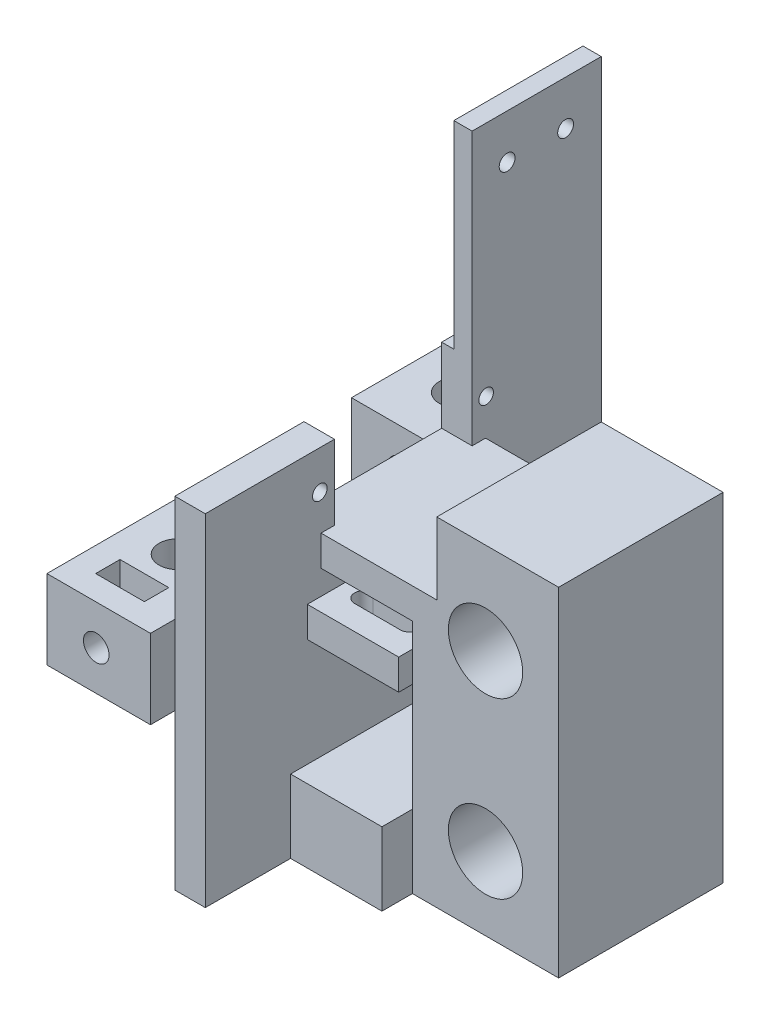
SolidWorks part; units mm, degrees
ref_plane "Front Plane" through (0, 0, 0) normal (0, 0, 1) x (1, 0, 0)
ref_plane "Top Plane" through (0, 0, 0) normal (0, 1, 0) x (1, 0, 0)
ref_plane "Right Plane" through (0, 0, 0) normal (1, 0, 0) x (0, 0, -1)
sketch "Sketch1" plane through (0, 0, 0) normal (0, 0, 1) x (1, 0, 0)
  line L0 (0, -26.25) -> (0, 26.25)
  line L1 (-28.3964, 0) -> (35.8693, 0) construction
  line L2 (0, 26.25) -> (24, 26.25)
  line L3 (24, 26.25) -> (24, -26.25)
  line L4 (24, -26.25) -> (0, -26.25)
  circle A0 centre (12, 14.25) radius 6.1
  circle A1 centre (12, -14.25) radius 6.1
  point P8 (0, 0)
  point P13 (12, 26.25)
  dimension "D2" = 12.2
  dimension "D1" = 26.25
  dimension "D3" = 28.5
  dimension "D4" = 12
extrude "Boss-Extrude1" add sketch "Sketch1" along normal mid plane 27
ref_plane "Plane1" through (0, 5.5, 0) normal (0, 1, 0) x (1, 0, 0)
sketch "Sketch2" plane through (0, 5.5, 0) normal (0, 1, 0) x (1, 0, 0)
  line L0 (0, 0) -> (-10.1748, 0) construction
  line L1 (0, 7) -> (0, -7)
  line L2 (0, 7) -> (-4, 7) construction
  line L3 (-4, 7) -> (-4, -7) construction
  line L4 (-4, -7) -> (0, -7) construction
  line L5 (0, 7) -> (-15, 7) construction
  line L6 (-15, 7) -> (-15, 15.75) construction
  line L7 (-15, 15.75) -> (0, 15.75) construction
  line L8 (-4, 7) -> (-11, 7)
  line L9 (-7.5, 7) -> (-7.5, 16.2228) construction
  line L10 (-11, 7) -> (-15, 7)
  line L11 (-15, 7) -> (-15, 15.75)
  line L12 (-15, 15.75) -> (0, 15.75)
  line L13 (0, 15.75) -> (0, 7)
  line L14 (-4, 7) -> (0, 7)
  line L15 (-11.25, 10.25) -> (-3.75, 10.25) construction
  line L16 (-11.25, 11.75) -> (-3.75, 11.75)
  line L17 (-11.25, 8.75) -> (-3.75, 8.75)
  line L18 (-15, -15.75) -> (0, -15.75) construction
  line L19 (-15, -7) -> (-15, -15.75) construction
  line L20 (0, -7) -> (-15, -7) construction
  line L21 (0, -7) -> (-4, -7) construction
  line L22 (-4, -7) -> (0, -7)
  line L23 (0, -15.75) -> (0, -7)
  line L24 (-15, -15.75) -> (0, -15.75)
  line L25 (-15, -7) -> (-15, -15.75)
  line L26 (-11, -7) -> (-15, -7)
  line L27 (-4, -7) -> (-11, -7)
  line L28 (-11.25, -10.25) -> (-3.75, -10.25) construction
  line L29 (-11.25, -11.75) -> (-3.75, -11.75)
  line L30 (-11.25, -8.75) -> (-3.75, -8.75)
  arc A0 (-11.25, 11.75) -> (-11.25, 8.75) centre (-11.25, 10.25) ccw
  arc A1 (-3.75, 8.75) -> (-3.75, 11.75) centre (-3.75, 10.25) ccw
  arc A2 (-11.25, -11.75) -> (-11.25, -8.75) centre (-11.25, -10.25) cw
  arc A3 (-3.75, -8.75) -> (-3.75, -11.75) centre (-3.75, -10.25) cw
  point P5 (0, 0)
  point P17 (-7.5, 10.25)
  point P28 (-7.5, -10.25)
  dimension "D3" = 4
  dimension "D1" = 14
  dimension "D2" = 7
  dimension "D4" = 3
  dimension "D5" = 1.75
extrude "Boss-Extrude2" add sketch "Sketch2" along normal blind 3 and the other way blind 2 contours L22 L27 L26 L25 L24 L23 L30 A3 L29 A2 | L8 L14 L13 L12 L11 L10 A1 L17 A0 L16
sketch "Sketch3" plane through (0, 0, 0) normal (-1, 0, 0) x (0, 0, 1)
  line L0 (-13.5, -8.25) -> (-13.5, -26.25)
  line L1 (-13.5, 3.5) -> (-13.5, -26.25) construction
  line L2 (-13.5, -26.25) -> (13.5, -26.25)
  line L3 (13.5, -26.25) -> (13.5, -8.25)
  line L4 (13.5, 3.5) -> (13.5, -26.25) construction
  line L5 (13.5, -8.25) -> (-13.5, -8.25)
  line L6 (-13.5, 26.25) -> (-13.5, 12.5)
  line L7 (-13.5, 26.25) -> (-13.5, 8.5) construction
  line L8 (-13.5, 12.5) -> (13.5, 12.5)
  line L9 (13.5, 26.25) -> (13.5, 8.5) construction
  line L10 (13.5, 12.5) -> (13.5, 26.25)
  line L11 (13.5, 26.25) -> (-13.5, 26.25)
  line L12 (-8.75, 8.5) -> (-8.75, 12.5)
  line L13 (-8.75, 8.5) -> (-7, 8.5)
  line L14 (-7, 8.5) -> (-7, 5.5)
  line L15 (14.85, 5.5) -> (-14.85, 5.5) construction
  line L16 (-7, 8.5) -> (-7, 3.5) construction
  line L17 (-7, 5.5) -> (7, 5.5)
  line L18 (7, 8.5) -> (7, 3.5) construction
  line L19 (7, 5.5) -> (7, 8.5)
  line L20 (7, 8.5) -> (8.75, 8.5)
  line L21 (13.5, 8.5) -> (7, 8.5) construction
  line L22 (8.75, 8.5) -> (8.75, 12.5)
  line M5 (-13.5, 26.25) -> (-13.5, 8.5)
  line M6 (-13.5, 8.5) -> (-7, 8.5)
  line M7 (-7, 8.5) -> (-7, 3.5)
  line M9 (-13.5, 3.5) -> (-13.5, -26.25)
  line M10 (-13.5, -26.25) -> (13.5, -26.25)
  line M11 (13.5, -26.25) -> (13.5, 3.5)
  line M13 (7, 3.5) -> (7, 8.5)
  line M14 (7, 8.5) -> (13.5, 8.5)
  line M15 (13.5, 8.5) -> (13.5, 26.25)
  line M16 (13.5, 26.25) -> (-13.5, 26.25)
  dimension "D1" = 1.75
extrude "Boss-Extrude3" add sketch "Sketch3" along normal up to surface (15 mm away) contours L8 M5 M15 M16 | L22 L8 L12 L17 M14 M6 M7 M13 | L5 M11 M9 M10 up to face at (-15, 6, -11.375)
sketch "Sketch4" plane through (-15, 0, 0) normal (-1, 0, 0) x (0, 0, 1)
  line L0 (-13.5, 26.25) -> (-13.5, -26.25)
  line L1 (-13.5, -26.25) -> (13.5, -26.25)
  line L2 (13.5, -26.25) -> (13.5, 26.25)
  line L3 (13.5, 26.25) -> (-13.5, 26.25)
  line L4 (-16, 29.5) -> (16, 29.5)
  line L5 (-16, 29.5) -> (-16, 17.5)
  line L6 (-16, 17.5) -> (16, 17.5)
  line L7 (16, 17.5) -> (16, 29.5)
  line L8 (-13.5, 12.5) -> (-8.75, 12.5) construction
  point P10 (0, 29.5)
  point P13 (0, 26.25)
  line M8 (13.5, 26.25) -> (-13.5, 26.25)
  line M9 (-15.75, 8.5) -> (-15.75, 3.5)
  dimension "D1" = 32
  dimension "D2" = 12
  dimension "D3" = 5
extrude "Cut-Extrude2" cut sketch "Sketch4" against normal blind 18 contours L6 L7 L4 L5 L2 M9 M8 | L6 L2 M9 M8
ref_plane "Plane2" through (-15, 0, 0) normal (-1, 0, 0) x (0, 0, 1)
sketch "Sketch6" plane through (-15, 0, 0) normal (-1, 0, 0) x (0, 0, 1)
  line L0 (-32.5, 29.75) -> (32.5, 29.75)
  line L1 (32.5, 29.75) -> (32.5, -26.25)
  line L2 (32.5, -26.25) -> (-32.5, -26.25)
  line L3 (-32.5, -26.25) -> (-32.5, 29.75)
  line L4 (13.5, 26.25) -> (-13.5, 26.25) construction
  line L8 (-13.5, -26.25) -> (13.5, -26.25) construction
  point P6 (0, 26.25)
  point P7 (0, 29.75)
  point P10 (0, -26.25)
  dimension "D1" = 65
  dimension "D2" = 56
extrude "Boss-Extrude4" add sketch "Sketch6" along normal blind 22
sketch "Sketch7" plane through (0, 29.75, 0) normal (0, 1, 0) x (1, 0, 0)
  line L0 (-29, 23) -> (-29, -23) construction
  line L1 (3, 11.3) -> (3, -11.3)
  line L2 (-15, -32.5) -> (-15, 32.5) construction
  line L3 (-15, -13.5) -> (-15, 13.5) construction
  line L4 (-37, 32.5) -> (-37, -32.5)
  line L5 (-15, 0) -> (7.9194, 0) construction
  line L6 (-15, 16) -> (-12.5, 16)
  line L7 (-27, 7.7) -> (-23.8, 7.7)
  line L8 (-27, 3.1) -> (-23.8, 3.1)
  line L9 (3, 11.3) -> (-12.5, 11.3)
  line L10 (-12.5, 11.3) -> (-12.5, 16)
  line L11 (-15, 16) -> (-15, -16)
  line L12 (-15, -16) -> (-12.5, -16)
  line L13 (-12.5, -11.3) -> (-12.5, -16)
  line L14 (3, -11.3) -> (-12.5, -11.3)
  line L15 (-15, 11.3) -> (-19.4, 11.3)
  line L16 (-19.4, 11.3) -> (-19.4, -11.3)
  line L17 (-19.4, -11.3) -> (-15, -11.3)
  line L18 (-19.4, 11.3) -> (-23.8, 11.3)
  line L19 (-23.8, 11.3) -> (-23.8, -3.4)
  line L20 (-23.8, -3.4) -> (-19.4, -3.4)
  line L21 (-23.8, 11.3) -> (-27, 11.3) construction
  line L22 (-27, 11.3) -> (-27, 5.4) construction
  line L23 (-27, 7.7) -> (-27, 3.1)
  circle A0 centre (-29, 23) radius 3.1
  circle A1 centre (-29, -23) radius 3.1
  point P4 (-37, 0)
  point P5 (-29, 0)
  point P26 (3, 0)
  point P37 (-27, 5.4)
  dimension "D1" = 6.2
  dimension "D2" = 6.2
  dimension "D3" = 46
  dimension "D4" = 16
  dimension "D5" = 4.4
  dimension "D6" = 11.3
  dimension "D7" = 15.5
  dimension "D8" = 3.2
  dimension "D9" = 5.9
  dimension "D10" = 4.6
  dimension "D11" = 4.4
  dimension "D12" = 14
extrude "Cut-Extrude3" cut sketch "Sketch7" against normal through all contours A0 | A1
sketch "Sketch8" plane through (0, 29.75, 0) normal (0, 1, 0) x (1, 0, 0)
  line L1 (-20, -32.5) -> (-37, -32.5)
  line L2 (-37, -32.5) -> (-37, 32.5)
  line L3 (-37, 32.5) -> (-20, 32.5)
  line L4 (-37, -32.5) -> (-15, -32.5) construction
  line L5 (-37, 32.5) -> (-15, 32.5) construction
  line L6 (-20, 32.5) -> (-20, -32.5)
  line L7 (-15, -13.5) -> (-15, 13.5) construction
  dimension "D1" = 5
extrude "Cut-Extrude4" cut sketch "Sketch8" against normal blind 17.5
sketch "Sketch10" plane through (0, -26.25, 0) normal (0, -1, 0) x (1, 0, 0)
  line L0 (-20, 32.5) -> (-37, 32.5) construction
  line L1 (-37, 32.5) -> (-37, -32.5) construction
  line L2 (-20, -32.5) -> (-20, 32.5) construction
  line L3 (-37, -32.5) -> (-20, -32.5) construction
  line L4 (-20, 32.5) -> (-37, 32.5)
  line L5 (-37, 32.5) -> (-37, -32.5)
  line L6 (-20, -32.5) -> (-20, 32.5)
  line L7 (-37, -32.5) -> (-20, -32.5)
sketch "Sketch11" plane through (-20, 0, 0) normal (-1, 0, 0) x (0, 0, 1)
  line L0 (-11.3, 29.75) -> (11.3, 29.75)
  line L1 (-32.5, 29.75) -> (32.5, 29.75) construction
  line L2 (-11.3, 29.75) -> (-11.3, 17.5)
  line L3 (-11.3, 17.5) -> (11.3, 17.5)
  line L4 (11.3, 17.5) -> (11.3, 29.75)
  point P2 (0, 29.75)
  point P5 (0, 29.75)
extrude "Cut-Extrude6" cut sketch "Sketch11" against normal up to surface (5 mm away) up to face at (-15, 9, 0)
sketch "Sketch12" plane through (0, 12.25, 0) normal (0, 1, 0) x (1, 0, 0)
  line L0 (-20, 13.5) -> (-37, 13.5)
  line L1 (-20, 32.5) -> (-20, -32.5) construction
  line L2 (-37, -32.5) -> (-37, 32.5) construction
  line L3 (-37, 13.5) -> (-37, -13.5)
  line L4 (-37, -13.5) -> (-20, -13.5)
  line L5 (-20, -13.5) -> (-20, 13.5)
extrude "Cut-Extrude7" cut sketch "Sketch12" against normal through all
sketch "Sketch13" plane through (0, -26.25, 0) normal (0, -1, 0) x (1, 0, 0)
  line L0 (-20, 32.5) -> (-37, 32.5) construction
  line L1 (-37, 32.5) -> (-37, -32.5) construction
  line L2 (-37, -32.5) -> (-20, -32.5) construction
  line L3 (-20, -32.5) -> (-20, 32.5) construction
  line L4 (-20, 32.5) -> (-37, 32.5)
  line L5 (-37, 32.5) -> (-37, -32.5)
  line L6 (-37, -32.5) -> (-20, -32.5)
  line L7 (-20, -32.5) -> (-20, 32.5)
extrude "Cut-Extrude8" cut sketch "Sketch13" against normal blind 25.5
sketch "Sketch16" plane through (0, -8.25, 0) normal (0, 1, 0) x (1, 0, 0)
  line L0 (0, -13.5) -> (-15, -13.5)
  line L2 (0, -13.5) -> (0, 13.5)
  line L3 (0, 13.5) -> (-15, 13.5)
  line L4 (-15, 13.5) -> (24, 13.5) construction
  line L5 (-15, -13.5) -> (-15, 13.5)
extrude "Cut-Extrude9" cut sketch "Sketch16" against normal blind 6
sketch "Sketch17" plane through (0, 0, -13.5) normal (0, 0, -1) x (-1, 0, 0)
  line L0 (0, -14.25) -> (0, -26.25)
  line L1 (15, -26.25) -> (-24, -26.25) construction
  line L2 (0, -26.25) -> (15, -26.25)
  line L3 (15, -26.25) -> (15, -14.25)
  line L4 (15, -14.25) -> (0, -14.25)
extrude "Boss-Extrude5" add sketch "Sketch17" along normal blind 5 and the other way blind 32
sketch "Sketch18" plane through (0, 0, -32.5) normal (0, 0, -1) x (-1, 0, 0)
  line L0 (28.9022, 25.3865) -> (28.9022, 12.25) construction
  line L1 (20, 12.25) -> (37, 12.25) construction
  line L2 (37, 12.25) -> (37, -0.75) construction
  line L3 (37, 5.75) -> (38.7662, 5.75) construction
  circle A0 centre (28.9022, 5.75) radius 2.1
  dimension "D1" = 4.2
  dimension "D2" = 0
  dimension "D3" = 0
sketch "Sketch19" plane through (0, 26.25, 0) normal (0, 1, 0) x (1, 0, 0)
  line L4 (3, 13.5) -> (3, -13.5)
  line L5 (3, -13.5) -> (24, -13.5)
  line L6 (24, -13.5) -> (24, 13.5)
  line L7 (24, 13.5) -> (3, 13.5)
  line L8 (3, 13.5) -> (3, -13.5)
  line L9 (3, -13.5) -> (24, -13.5)
  line L10 (24, -13.5) -> (24, 13.5)
  line L11 (24, 13.5) -> (3, 13.5)
  dimension "D1" = 0
extrude "Boss-Extrude6" add sketch "Sketch19" along normal blind 3.05
sketch "Sketch20" plane through (0, 0, 13.5) normal (0, 0, 1) x (1, 0, 0)
  line L0 (3, 17.5) -> (4, 17.5)
  line L1 (4, 17.5) -> (4, 29.3)
  line L2 (3, 29.3) -> (24, 29.3) construction
  line L3 (4, 29.3) -> (3, 29.3)
  line L4 (3, 29.3) -> (3, 17.5)
extrude "Cut-Extrude11" cut sketch "Sketch20" against normal through all
sketch "Sketch21" plane through (-15, 0, 0) normal (1, 0, 0) x (0, 0, -1)
  circle A0 centre (-13.7, 23.4) radius 1.2
  circle A1 centre (13.6, 23.4) radius 1.2
extrude "Cut-Extrude12" cut sketch "Sketch21" against normal blind 10
ref_plane "Plane3" through (0, 12.25, 0) normal (0, 1, 0) x (1, 0, 0)
sketch "Sketch22" plane through (0, 12.25, 0) normal (0, 1, 0) x (1, 0, 0)
  line L0 (-29, 23) -> (-29, 34.5) construction
  line L2 (-29, 30.5) -> (-29, 34.5) construction
  line L3 (-25, 30.5) -> (-33, 30.5)
  line L4 (-29, 30.5) -> (-29, 33.0319) construction
  line L5 (-25, 30.5) -> (-25, 34.5)
  line L7 (-33, 34.5) -> (-33, 30.5)
  line L8 (0, 0) -> (-75.4132, 0) construction
  line L9 (-33, -34.5) -> (-33, -30.5)
  line L10 (-25, -34.5) -> (-33, -34.5)
  line L11 (-25, -30.5) -> (-25, -34.5)
  line L12 (-25, -30.5) -> (-33, -30.5)
  line L13 (-25, 34.5) -> (-33, 34.5)
  dimension "D1" = 0
  dimension "D2" = 4
  dimension "D3" = 7.5
sketch "Sketch23" plane through (0, 0, -32.5) normal (0, 0, -1) x (-1, 0, 0)
  line L0 (20, -0.75) -> (20, 12.25)
  line L1 (9.35, 12.25) -> (-9.35, 12.25) construction
  line L2 (20, 12.25) -> (37, 12.25)
  line L3 (37, 12.25) -> (37, -0.75) construction
  line L4 (37, 12.25) -> (37, -0.75)
  line L5 (37, -0.75) -> (20, -0.75)
extrude "Boss-Extrude7" add sketch "Sketch23" along normal blind 4
sketch "Sketch24" plane through (0, 0, 32.5) normal (0, 0, 1) x (1, 0, 0)
  line L0 (-37, 12.25) -> (-37, -0.75)
  line L1 (-37, -0.75) -> (-20, -0.75)
  line L2 (-20, -0.75) -> (-20, 12.25)
  line L3 (0, 12.25) -> (-75.4132, 12.25) construction
  line L4 (-20, 12.25) -> (-37, 12.25)
extrude "Boss-Extrude8" add sketch "Sketch24" along normal blind 4
sketch "Sketch25" plane through (0, 0, -36.5) normal (0, 0, -1) x (-1, 0, 0)
  circle A0 centre (28.9022, 5.75) radius 2.1 construction
  circle A1 centre (28.9022, 5.75) radius 2.1
extrude "Cut-Extrude14" cut sketch "Sketch25" against normal through all
sketch "Sketch26" plane through (0, 12.25, 0) normal (0, 1, 0) x (1, 0, 0)
  line L8 (-33, -32.5) -> (-33, -28.5)
  line L9 (-25, -28.5) -> (-33, -28.5)
  line L10 (-25, -32.5) -> (-33, -32.5)
  line L11 (-25, -28.5) -> (-25, -32.5)
  line L12 (-25, 28.5) -> (-25, 32.5)
  line L13 (-25, 28.5) -> (-33, 28.5)
  line L14 (-33, 32.5) -> (-33, 28.5)
  line L15 (-25, 32.5) -> (-33, 32.5)
  line L16 (-37, 36.5) -> (-20, 36.5) construction
  line L17 (-20, -36.5) -> (-37, -36.5) construction
  dimension "D1" = 8
  dimension "D2" = 4
  dimension "D3" = 4
  dimension "D4" = 8
  dimension "D5" = 4
  dimension "D6" = 4
extrude "Cut-Extrude15" cut sketch "Sketch26" against normal through all
sketch "Sketch27" plane through (0, 29.75, 0) normal (0, 1, 0) x (1, 0, 0)
  line L8 (-18, 32.5) -> (-18, 11.3)
  line L9 (-18, 11.3) -> (-15, 11.3)
  line L10 (-15, 11.3) -> (-15, 32.5)
  line L11 (-15, 32.5) -> (-18, 32.5)
extrude "Boss-Extrude9" add sketch "Sketch27" along normal blind 32.5
sketch "Sketch28" plane through (-18, 0, 0) normal (-1, 0, 0) x (0, 0, 1)
  circle A0 centre (-26.65, 54.95) radius 1.3
  circle A1 centre (-17.05, 54.95) radius 1.3
  dimension "D1" = 2.6
  dimension "D2" = 2.6
extrude "Cut-Extrude16" cut sketch "Sketch28" against normal through all
sketch "Sketch29" plane through (0, 0, 13.5) normal (0, 0, 1) x (1, 0, 0)
  line L0 (4, 29.3) -> (4, -26.25)
  line L1 (0, -26.25) -> (24, -26.25) construction
  line L2 (4, -26.25) -> (24, -26.25)
  line L3 (24, -26.25) -> (24, 29.3)
  line L4 (24, 29.3) -> (4, 29.3)
extrude "Boss-Extrude10" [suppressed] add sketch "Sketch29" along normal blind 26.5
